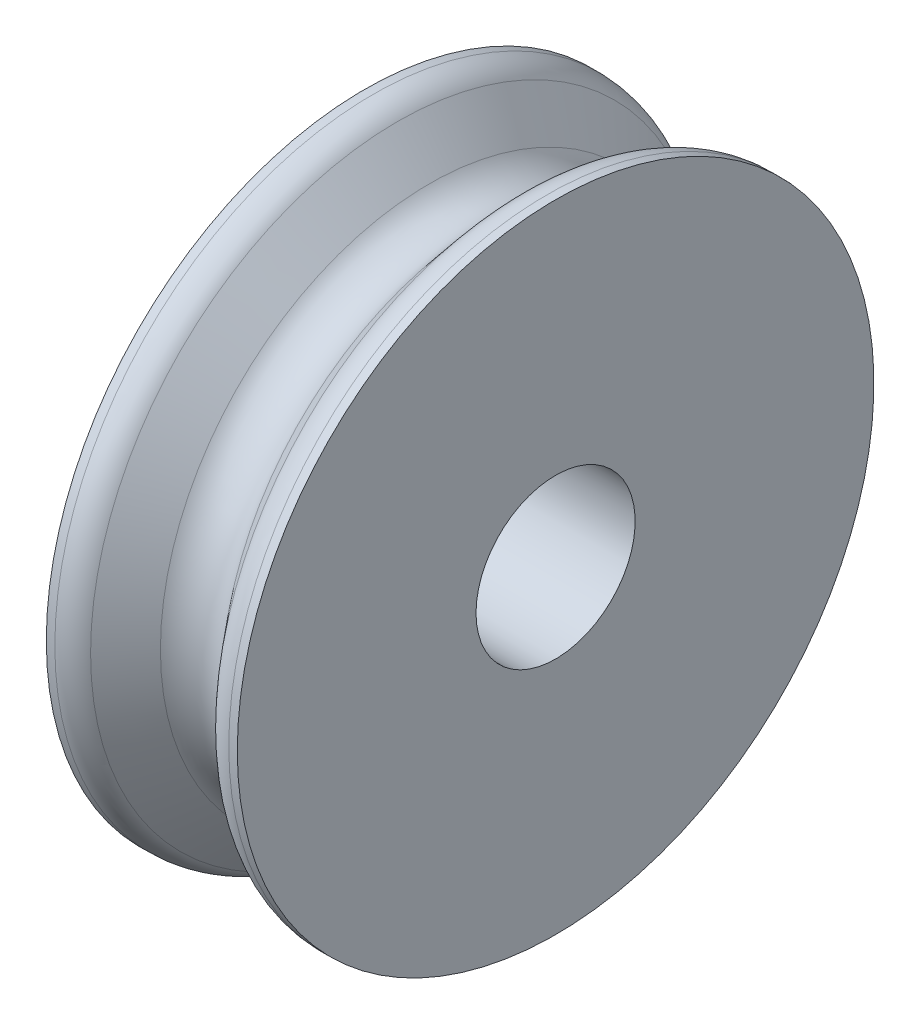
SolidWorks part; units mm, degrees
ref_plane "Front Plane" through (0, 0, 0) normal (0, 0, 1) x (1, 0, 0)
ref_plane "Top Plane" through (0, 0, 0) normal (0, 1, 0) x (1, 0, 0)
ref_plane "Right Plane" through (0, 0, 0) normal (1, 0, 0) x (0, 0, -1)
sketch "Sketch1" plane through (0, 0, 0) normal (0, 0, 1) x (1, 0, 0)
  line L1 (-11.3287, 50) -> (-15, 50)
  line L2 (-15, 50) -> (-15, 12.5)
  line L5 (-15, 12.5) -> (0, 12.5)
  line L6 (0, 12.5) -> (0, 40)
  line L10 (-11.3287, 50) -> (-4.8261, 42.2504)
  line L11 (-75.8883, 0) -> (71.8055, 0) construction
  arc A0 (-4.8261, 42.2504) -> (0, 40) centre (0, 46.3) ccw
  dimension "D3" = 6.3
  dimension "D1" = 40
  dimension "D2" = 15
  dimension "D4" = 50
  dimension "D5" = 40
  dimension "D6" = 12.5
revolve "Revolve1" add sketch "Sketch1" angle 360 about L11
mirror "Mirror1" about plane through (0, 12.5, 0) normal (-1, 0, 0) of "Revolve1"
fillet "Fillet1" radius 5 2 edges at (11.3287, 0, 50) (-11.3287, 0, 50)
ref_plane "Plane1" through (0, 40, 0) normal (0, 1, 0) x (1, 0, 0)
